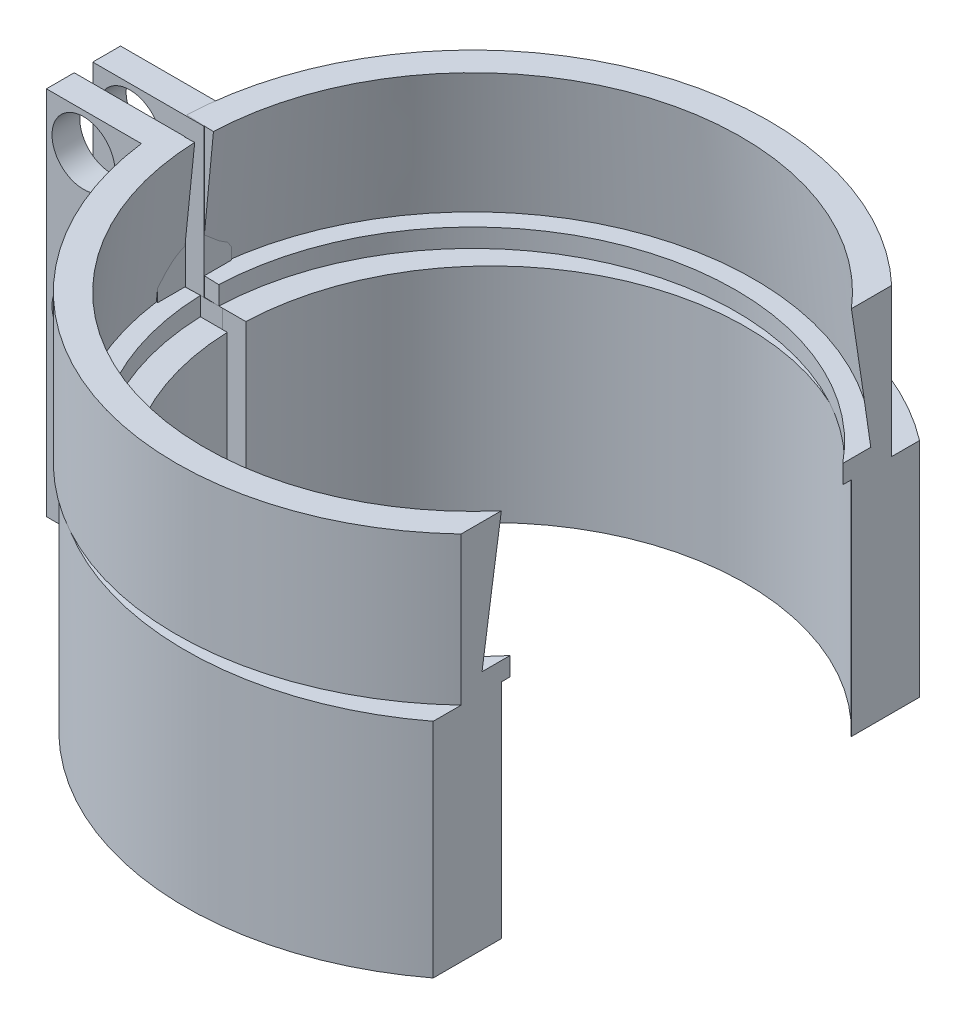
SolidWorks part; units mm, degrees
ref_plane "Front Plane" through (0, 0, 0) normal (0, 0, 1) x (1, 0, 0)
ref_plane "Top Plane" through (0, 0, 0) normal (0, 1, 0) x (1, 0, 0)
ref_plane "Right Plane" through (0, 0, 0) normal (1, 0, 0) x (0, 0, -1)
sketch "Sketch1" plane through (0, 0, 0) normal (0, 1, 0) x (1, 0, 0)
  line L0 (-13.7408, 0.5018) -> (-14.9977, 0.5)
  line L1 (-13.7408, -0.5018) -> (-14.9977, -0.5)
  line L2 (0, 0) -> (7.6847, 0) construction
  line L3 (-14.9977, 0.5) -> (-22, 0.5)
  line L4 (-22, 0.5) -> (-22, 2)
  line L5 (-22, 2) -> (-16.3783, 2)
  line L6 (-14.9977, -0.5) -> (-22, -0.5)
  line L7 (-22, -0.5) -> (-22, -2)
  line L8 (-22, -2) -> (-16.3783, -2)
  arc A0 (-6.875, -11.9078) -> (-6.875, 11.9078) centre (0, 0) ccw
  arc A1 (-8.25, -14.2894) -> (-8.25, 14.2894) centre (0, 0) ccw
  arc A2 (-6.875, 11.9078) -> (-13.7408, 0.5018) centre (0, 0) ccw
  arc A3 (-8.25, 14.2894) -> (-16.3783, 2) centre (0, 0) ccw
  arc A4 (-16.3783, -2) -> (-8.25, -14.2894) centre (0, 0) ccw
  arc A5 (-13.7408, -0.5018) -> (-6.875, -11.9078) centre (0, 0) ccw
  dimension "D1" = 27.5
  dimension "D2" = 1.5
  dimension "D4" = 16.5
  dimension "D3" = 0.5
  dimension "D5" = 22
  dimension "D6" = 0.5
  dimension "D7" = 22
  dimension "D8" = 1.5
extrude "Boss-Extrude1" add sketch "Sketch1" along normal blind 12
ref_plane "Plane1" through (-1, 0, 0) normal (1, 0, 0) x (0, 0, -1)
sketch "Sketch3" plane through (-1, 0, 0) normal (1, 0, 0) x (0, 0, -1)
  line L0 (0, 12) -> (-15, 12) construction
  line L1 (16.5, 12) -> (-16.5, 12) construction
  line L2 (-16, 12) -> (-16, 20)
  line L3 (-16, 20) -> (-14.5, 20)
  line L4 (-14.5, 20) -> (-15.2, 13)
  line L5 (-16, 12) -> (-15, 12)
  line L6 (0, 12) -> (0, 22.5005) construction
  line L7 (-15, 12) -> (-14.2, 12)
  line L8 (-14.2, 12) -> (-14.2, 13)
  line L9 (-14.2, 13) -> (-15.2, 13)
  dimension "D1" = 15
  dimension "D2" = 8
  dimension "D3" = 14.5
  dimension "D4" = 0.8
  dimension "D5" = 1
  dimension "D6" = 15.2
  dimension "D7" = 16
revolve "Revolve1" add sketch "Sketch3" angle 268 about L6 other way angle 88
sketch "Sketch4" plane through (0, 0, -2) normal (0, 0, -1) x (-1, 0, 0)
  line L0 (16.8745, 12) -> (22, 12) construction
  line L2 (22, 12) -> (22, 0) construction
  line L3 (16.3783, 0) -> (22, 0) construction
  circle A0 centre (20, 10) radius 1.7
  circle A1 centre (18.4552, 2.5) radius 1.7
  dimension "D1" = 3.4
  dimension "D4" = 3.4
  dimension "D2" = 2
  dimension "D3" = 2
  dimension "D5" = 2.5
extrude "Cut-Extrude1" cut sketch "Sketch4" against normal through all both and the other way through all
sketch "Sketch5" plane through (0, 0, 2) normal (0, 0, 1) x (1, 0, 0)
  line L0 (-22, 12) -> (-22, 20)
  line L1 (-22, 20) -> (-16, 20)
  line L2 (-16, 20) -> (-16, 12)
  line L3 (-16, 12) -> (-22, 12)
  line L4 (-1, -6.6) -> (-1, 6.6) construction
  circle A0 centre (-20, 18) radius 1.7
  dimension "D1" = 3.4
  dimension "D2" = 2
  dimension "D3" = 2
  dimension "D4" = 15
  dimension "D5" = 4
extrude "Boss-Extrude3" add sketch "Sketch5" against normal blind 1.5
sketch "Sketch6" plane through (0, 0, -2) normal (0, 0, -1) x (-1, 0, 0)
  line L0 (1, 6.6) -> (1, -6.6) construction
  line L1 (16, 12) -> (22, 12)
  line L2 (16, 12) -> (16, 20)
  line L3 (16, 20) -> (22, 20)
  line L4 (22, 12) -> (22, 20)
  circle A0 centre (20, 18) radius 1.7 construction
  circle A1 centre (20, 18) radius 1.7
  dimension "D1" = 15
  dimension "D2" = 21
extrude "Boss-Extrude6" add sketch "Sketch6" against normal blind 1.5 separate body
sketch "Sketch7" plane through (0, 0, 0) normal (0, -1, 0) x (1, 0, 0)
  line L1 (16.5, 0) -> (16.5, -11.1611) construction
  line L2 (9.9999, 15.5395) -> (20.4007, 15.5395)
  line L3 (9.9999, 15.5395) -> (14.9999, 15.5395) construction
  line L4 (9.9999, 15.5395) -> (9.9999, -13.7021)
  line L5 (9.9999, -13.7021) -> (14.9999, -13.7021) construction
  line L6 (14.9999, 15.5395) -> (14.9999, -13.7021) construction
  line L7 (9.9999, -13.7021) -> (9.9999, 15.5395) construction
  line L8 (9.9999, -13.7021) -> (20.4007, -13.7021)
  line L9 (20.4007, 15.5395) -> (20.4007, -13.7021)
  arc A0 (-16.3783, -2) -> (-16.3783, 2) centre (0, 0) ccw construction
extrude "Cut-Extrude2" cut sketch "Sketch7" against normal through all
